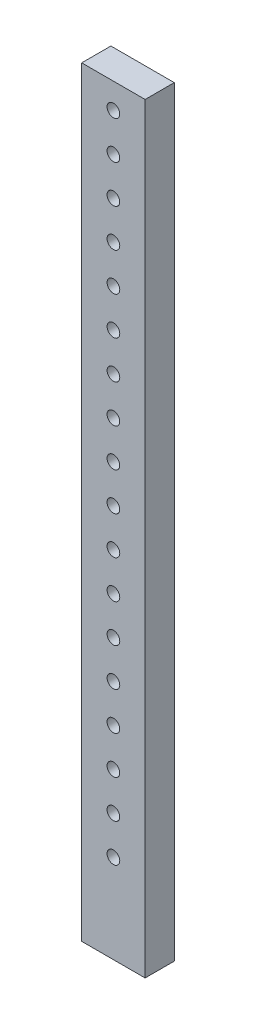
SolidWorks part; units mm, degrees
ref_plane "Front Plane" through (0, 0, 0) normal (0, 0, 1) x (1, 0, 0)
ref_plane "Top Plane" through (0, 0, 0) normal (0, 1, 0) x (1, 0, 0)
ref_plane "Right Plane" through (0, 0, 0) normal (1, 0, 0) x (0, 0, -1)
sketch "Sketch2" plane through (0, 0, 0) normal (0, 0, 1) x (1, 0, 0)
  line L0 (0, 377.7492) -> (0, -315.4314) construction
  line L1 (-25, 300) -> (25, 300)
  line L2 (-25, 300) -> (-25, -300)
  line L3 (-25, -300) -> (25, -300)
  line L4 (25, 300) -> (25, -300)
  line L5 (-25, 300) -> (25, -300) construction
  line L6 (-25, -300) -> (25, 300) construction
  circle A0 centre (0, 280) radius 5
  circle A1 centre (0, 250) radius 5
  circle A2 centre (0, 220) radius 5
  circle A3 centre (0, 190) radius 5
  circle A4 centre (0, 160) radius 5
  circle A5 centre (0, 130) radius 5
  circle A6 centre (0, 100) radius 5
  circle A7 centre (0, 70) radius 5
  circle A8 centre (0, 40) radius 5
  circle A9 centre (0, 10) radius 5
  circle A10 centre (0, -20) radius 5
  circle A11 centre (0, -50) radius 5
  circle A12 centre (0, -80) radius 5
  circle A13 centre (0, -110) radius 5
  circle A14 centre (0, -140) radius 5
  circle A15 centre (0, -170) radius 5
  circle A16 centre (0, -200) radius 5
  circle A17 centre (0, -230) radius 5
  point P0 (0, 0)
  dimension "D3" = 18
  dimension "D4" = 10
  dimension "D1" = 600
  dimension "D2" = 50
  dimension "D5" = 20
extrude "Boss-Extrude1" add sketch "Sketch2" along normal blind 23
